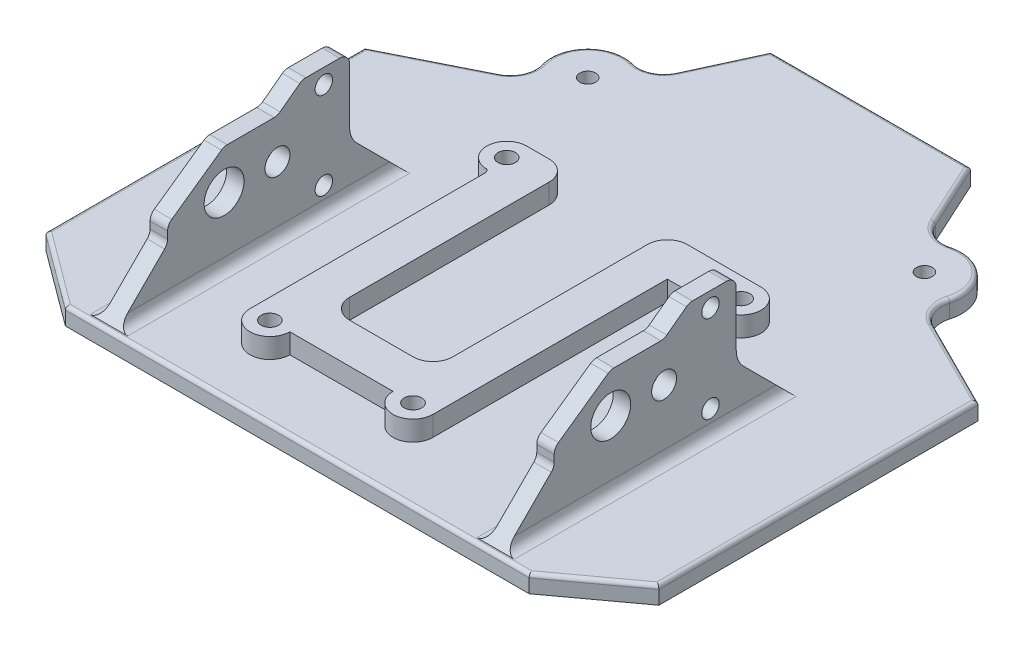
SolidWorks part; units mm, degrees
ref_plane "Front Plane" through (0, 0, 0) normal (0, 0, 1) x (1, 0, 0)
ref_plane "Top Plane" through (0, 0, 0) normal (0, 1, 0) x (1, 0, 0)
ref_plane "Right Plane" through (0, 0, 0) normal (1, 0, 0) x (0, 0, -1)
sketch "Sketch1" plane through (0, 0, 0) normal (0, 1, 0) x (1, 0, 0)
  line L0 (0, 0) -> (63, 0)
  line L1 (0, 0) -> (-30, 0)
  line L2 (63, 0) -> (93, 0)
  line L3 (0, 90) -> (-30, 75)
  line L4 (31.5, 115) -> (11.5, 115)
  line L5 (0, 0) -> (0, 90) construction
  line L6 (0, 90) -> (11.5, 115)
  line L7 (31.5, 80) -> (4.5, 80) construction
  line L8 (4.5, 80) -> (4.5, 10) construction
  line L9 (4.5, 10) -> (58.5, 10) construction
  line L10 (58.5, 10) -> (58.5, 80) construction
  line L11 (58.5, 80) -> (31.5, 80) construction
  line L12 (63, 90) -> (63, 0) construction
  line L13 (31.5, 115) -> (51.5, 115)
  line L14 (51.5, 115) -> (63, 90)
  line L15 (-30, 0) -> (-30, 75)
  line L16 (-9.017, 11.0041) -> (-9.017, 42.3041) construction
  line L17 (-13.9063, 42.3041) -> (-3.8424, 42.3041) construction
  line L18 (93, 75) -> (93, 0)
  line L19 (63, 90) -> (93, 75)
  line L20 (-9.017, 47.5041) -> (-5.517, 47.5041) construction
  line L21 (-5.517, 47.5041) -> (-5.517, 11.0041) construction
  line L22 (-9.017, 11.0041) -> (-27.517, 11.0041) construction
  line L23 (-27.517, 11.0041) -> (-27.517, 19.5041) construction
  line L24 (-27.517, 47.5041) -> (-9.017, 47.5041) construction
  line L25 (-9.017, 47.5041) -> (-9.017, 24.8541) construction
  line L26 (-9.017, 47.5041) -> (-9.017, 76.0041) construction
  line L27 (-9.017, 76.0041) -> (-27.517, 76.0041) construction
  line L28 (-27.517, 47.5041) -> (-27.517, 76.0041) construction
  line L29 (-27.517, 24.8541) -> (-38.667, 24.8541) construction
  line L30 (-9.017, 24.8541) -> (0.983, 24.8541) construction
  line L31 (0.983, 24.8541) -> (0.983, 19.5041) construction
  line L32 (0.983, 19.5041) -> (-9.017, 19.5041) construction
  line L33 (-27.517, 24.8541) -> (-27.517, 47.5041) construction
  line L34 (-9.017, 19.5041) -> (-9.017, 11.0041) construction
  line L35 (-38.667, 24.8541) -> (-38.667, 19.5041) construction
  line L36 (-38.667, 19.5041) -> (-27.517, 19.5041) construction
  line L37 (31.5, 115) -> (31.5, 0) construction
  line L38 (90.517, 47.5041) -> (72.017, 47.5041) construction
  line L39 (90.517, 47.5041) -> (90.517, 76.0041) construction
  line L40 (72.017, 76.0041) -> (90.517, 76.0041) construction
  line L41 (72.017, 47.5041) -> (72.017, 76.0041) construction
  line L42 (90.517, 24.8541) -> (90.517, 47.5041) construction
  line L43 (90.517, 24.8541) -> (101.667, 24.8541) construction
  line L44 (101.667, 24.8541) -> (101.667, 19.5041) construction
  line L45 (101.667, 19.5041) -> (90.517, 19.5041) construction
  line L46 (90.517, 11.0041) -> (90.517, 19.5041) construction
  line L47 (72.017, 11.0041) -> (90.517, 11.0041) construction
  line L48 (72.017, 19.5041) -> (72.017, 11.0041) construction
  line L49 (62.017, 19.5041) -> (72.017, 19.5041) construction
  line L50 (62.017, 24.8541) -> (62.017, 19.5041) construction
  line L51 (72.017, 24.8541) -> (62.017, 24.8541) construction
  line L52 (72.017, 47.5041) -> (72.017, 24.8541) construction
  line L53 (-5.517, 11.0041) -> (-9.017, 11.0041) construction
  line L54 (68.517, 11.0041) -> (72.017, 11.0041) construction
  line L55 (68.517, 47.5041) -> (68.517, 11.0041) construction
  line L56 (72.017, 47.5041) -> (68.517, 47.5041) construction
  line L57 (76.9063, 42.3041) -> (66.8424, 42.3041) construction
extrude "Boss-Extrude1" add sketch "Sketch1" along normal blind 3.5
sketch "Sketch2" plane through (0, 3.5, 0) normal (0, 1, 0) x (1, 0, 0)
  line L0 (-9.017, 47.5041) -> (-5.517, 47.5041)
  line L1 (-5.517, 47.5041) -> (-5.517, 11.0041)
  line L2 (-5.517, 11.0041) -> (-9.017, 11.0041)
  line L3 (-9.017, 11.0041) -> (-9.017, 47.5041)
  line L4 (68.517, 11.0041) -> (68.517, 47.5041)
  line L5 (68.517, 47.5041) -> (72.017, 47.5041)
  line L6 (72.017, 47.5041) -> (72.017, 11.0041)
  line L7 (72.017, 11.0041) -> (68.517, 11.0041)
extrude "Boss-Extrude2" add sketch "Sketch2" along normal blind 25
chamfer "Chamfer1" distance 10 angle 45 4 edges at (-7.267, 3.5, -47.5041) (-7.267, 3.5, -11.0041) (70.267, 3.5, -47.5041) (70.267, 3.5, -11.0041)
fillet "Fillet1" radius 2 2 edges at (68.517, 3.5, -29.2541) (-5.517, 3.5, -29.2541)
sketch "Sketch3" plane through (72.017, 0, 0) normal (1, 0, 0) x (0, 0, -1)
  circle A0 centre (42.3398, 25.5) radius 1.75
  circle A1 centre (42.3398, 8) radius 1.75
extrude "Cut-Extrude1" cut sketch "Sketch3" against normal blind 108
fillet "Fillet2" radius 2 2 edges at (-9.017, 3.5, -29.2541) (72.017, 3.5, -29.2541)
sketch "Sketch4" plane through (72.017, 0, 0) normal (1, 0, 0) x (0, 0, -1)
  circle A0 centre (22.3398, 16.75) radius 4
  circle A1 centre (33.0398, 16.75) radius 2.5
extrude "Cut-Extrude2" cut sketch "Sketch4" against normal blind 108
sketch "Sketch5" plane through (72.017, 0, 0) normal (1, 0, 0) x (0, 0, -1)
  line L0 (22.3398, 24.7475) -> (11.0041, 16.75)
  line L1 (22.3398, 24.7475) -> (33.0398, 24.7475)
  line L2 (33.0398, 24.7475) -> (38.0603, 28.5)
  line L3 (11.0041, 28.5) -> (47.5041, 28.5) construction
  line L4 (11.0041, 16.75) -> (11.0041, 28.5)
  line L5 (11.0041, 28.5) -> (38.0603, 28.5)
extrude "Cut-Extrude3" cut sketch "Sketch5" against normal blind 108
fillet "Fillet3" radius 2 12 edges at (70.267, 28.5, -38.0603) (70.267, 24.7475, -33.0398) (70.267, 24.7475, -22.3398) (70.267, 16.75, -11.0041) (70.267, 13.5, -11.0041) (-7.267, 13.5, -11.0041) (-7.267, 16.75, -11.0041) (-7.267, 24.7475, -22.3398) (-7.267, 28.5, -38.0603) (-7.267, 24.7475, -33.0398) (-7.267, 28.5, -47.5041) (70.267, 28.5, -47.5041)
fillet "Fillet4" radius 5 2 edges at (-7.267, 13.5, -47.5041) (70.267, 13.5, -47.5041)
sketch "Sketch6" plane through (0, 3.5, 0) normal (0, 1, 0) x (1, 0, 0)
  line L0 (16, 14) -> (36.7, 14)
  line L1 (16, 66) -> (16, 26)
  line L2 (20, 22) -> (32.7, 22)
  line L3 (36.7, 26) -> (36.7, 65)
  line L4 (7.5, 70) -> (12, 70)
  line L13 (8, 14) -> (8, 61.0947)
  line L15 (55.5, 69) -> (40.7, 69)
  line L18 (44.7, 14) -> (44.7, 61)
  line L19 (44.7, 61) -> (55.5, 61)
  circle A0 centre (12, 14) radius 1.75
  circle A1 centre (40.7, 14) radius 1.75
  circle A2 centre (7.5, 66) radius 1.75
  circle A3 centre (55.5, 65) radius 1.75
  arc A4 (7.5, 70) -> (7.5, 62) centre (7.5, 66) ccw
  arc A5 (55.5, 61) -> (55.5, 69) centre (55.5, 65) ccw
  arc A6 (36.7, 14) -> (44.7, 14) centre (40.7, 14) ccw
  arc A7 (8, 14) -> (16, 14) centre (12, 14) ccw
  arc A8 (7.5, 62) -> (8, 61) centre (6.8447, 61.0473) cw
  arc A9 (16, 26) -> (20, 22) centre (20, 26) ccw
  arc A10 (32.7, 22) -> (36.7, 26) centre (32.7, 26) ccw
  arc A11 (36.7, 65) -> (40.7, 69) centre (40.7, 65) cw
  arc A12 (12, 70) -> (16, 66) centre (12, 66) cw
  point P29 (16, 69)
  dimension "D1" = 4
  dimension "D2" = 4
extrude "Boss-Extrude3" add sketch "Sketch6" along normal blind 4 contours A4 A8 L13 A7 L0 A6 L18 L19 A5 L15 A0 A1 A2 A3
sketch "Sketch7" plane through (0, 7.5, 0) normal (0, 1, 0) x (1, 0, 0)
  circle A0 centre (7.5, 66) radius 1.75
  circle A1 centre (55.5, 65) radius 1.75
  circle A2 centre (40.7, 14) radius 1.75
  circle A3 centre (12, 14) radius 1.75
extrude "Cut-Extrude4" cut sketch "Sketch7" against normal blind 37
chamfer "Chamfer2" distance 2.5 distance2 2 4 edges at (7.5, 0, -67.75) (55.5, 0, -66.75) (40.7, 0, -15.75) (12, 0, -15.75)
sketch "Sketch8" plane through (0, 3.5, 0) normal (0, 1, 0) x (1, 0, 0)
  line L0 (-30, 11.1123) -> (-15, 0)
  line L1 (-30, 0) -> (-30, 75) construction
  line L2 (0, 0) -> (-30, 0) construction
  line L3 (78, 0) -> (93, 11.0041)
  line L4 (63, 0) -> (93, 0) construction
  line L5 (93, 75) -> (93, 0) construction
  line L6 (93, 11.0041) -> (93, 0)
  line L7 (93, 0) -> (78, 0)
  line L8 (-30, 11.1123) -> (-30, 0)
  line L9 (-30, 0) -> (-15, 0)
extrude "Cut-Extrude5" cut sketch "Sketch8" against normal blind 37
sketch "Sketch9" plane through (0, 3.5, 0) normal (0, 1, 0) x (1, 0, 0)
  line L0 (-7.2304, 86.3848) -> (0, 90)
  line L2 (0, 90) -> (3.2576, 97.0816)
  line L4 (59.7424, 97.0816) -> (63, 90)
  line L6 (63, 90) -> (70.2304, 86.3848)
  circle A0 centre (-2.2585, 92) radius 1.6
  circle A1 centre (65.2585, 92) radius 1.6
  arc A2 (-2.2585, 99.5) -> (-9.7585, 92) centre (-2.2585, 92) ccw
  arc A3 (72.7585, 92) -> (65.2585, 99.5) centre (65.2585, 92) ccw
  arc A4 (3.2576, 97.0816) -> (-7.2304, 86.3848) centre (-2.2585, 92) ccw
  arc A5 (70.2304, 86.3848) -> (59.7424, 97.0816) centre (65.2585, 92) ccw
extrude "Boss-Extrude4" add sketch "Sketch9" against normal blind 3.5
fillet "Fillet5" radius 5 4 edges at (59.7424, 1.75, -97.0816) (70.2304, 1.75, -86.3848) (3.2576, 1.75, -97.0816) (-7.2304, 1.75, -86.3848)
fillet "Fillet6" radius 0.75 16 edges at (54.4932, 3.5, -108.493) (59.903, 3.5, -99.55) (70.6285, 3.5, -97.2358) (72.6634, 3.5, -86.4717) (8.5068, 3.5, -108.493) (3.097, 3.5, -99.55) (-7.6285, 3.5, -97.2358) (-9.6634, 3.5, -86.4717) (31.5, 3.5, -115) (84.0062, 3.5, -79.4969) (-21.0062, 3.5, -79.4969) (-30, 3.5, -43.0562) (-22.5, 3.5, -5.5562) (31.5, 3.5, 0) (93, 3.5, -43.002) (85.5, 3.5, -5.502)
